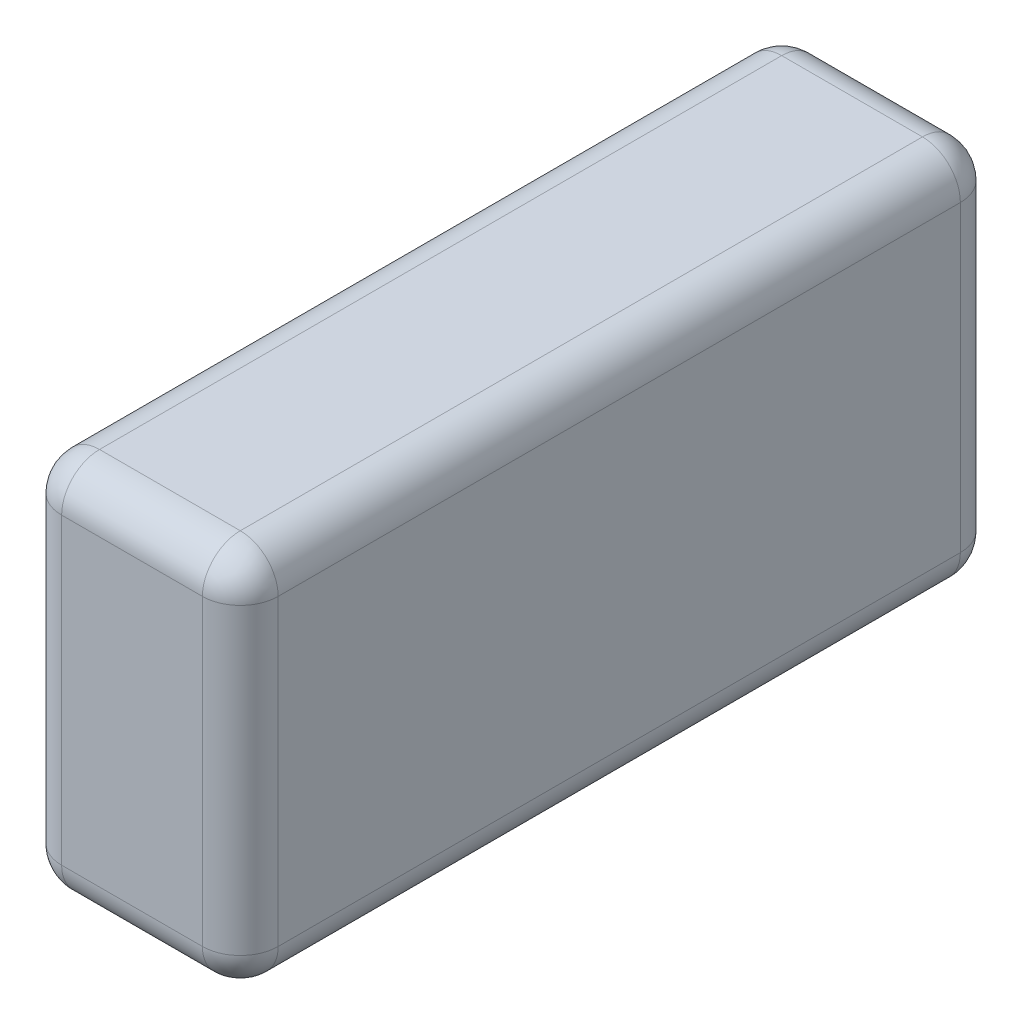
SolidWorks part; units mm, degrees
ref_plane "Front Plane" through (0, 0, 0) normal (0, 0, 1) x (1, 0, 0)
ref_plane "Top Plane" through (0, 0, 0) normal (0, 1, 0) x (1, 0, 0)
ref_plane "Right Plane" through (0, 0, 0) normal (1, 0, 0) x (0, 0, -1)
sketch "Sketch1" plane through (0, 0, 0) normal (1, 0, 0) x (0, 0, -1)
  line L1 (-350, 205.4979) -> (350, 205.4979)
  line L2 (-350, 205.4979) -> (-350, -144.5021)
  line L3 (-350, -144.5021) -> (350, -144.5021)
  line L4 (350, 205.4979) -> (350, -144.5021)
  line L5 (-350, 205.4979) -> (350, -144.5021) construction
  line L6 (-350, -144.5021) -> (350, 205.4979) construction
  point P0 (0, 0)
  point P5 (-350, -144.5021)
  dimension "D1" = 700
  dimension "D2" = 350
extrude "Boss-Extrude1" add sketch "Sketch1" along normal blind 200
fillet "Fillet1" radius 35 12 edges at (100, 205.4979, -350) (100, 205.4979, 350) (100, -144.5021, 350) (100, -144.5021, -350) (200, -144.5021, 0) (200, 30.4979, 350) (200, 205.4979, 0) (200, 30.4979, -350) (0, 205.4979, 0) (0, 30.4979, 350) (0, -144.5021, 0) (0, 30.4979, -350)
